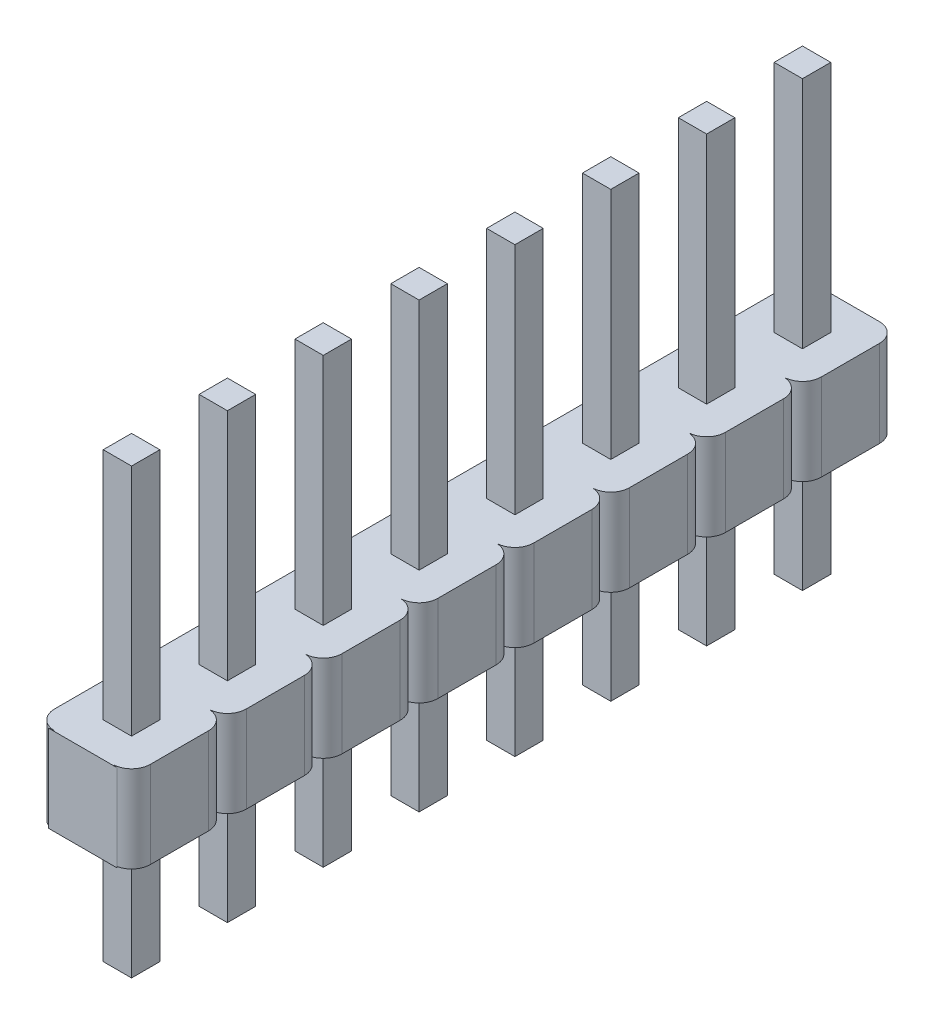
SolidWorks part; units mm, degrees
ref_plane "Alzado" through (0, 0, 0) normal (0, 0, 1) x (1, 0, 0)
ref_plane "Planta" through (0, 0, 0) normal (0, 1, 0) x (1, 0, 0)
ref_plane "Vista lateral" through (0, 0, 0) normal (1, 0, 0) x (0, 0, -1)
ref_plane "Plano1" through (0, 2.3, 0) normal (0, 1, 0) x (1, 0, 0)
sketch "Croquis1" plane through (0, 2.3, 0) normal (0, 1, 0) x (1, 0, 0)
  line L0 (-1.27, -19.07) -> (1.27, -19.07)
  line L1 (1.27, -19.07) -> (1.27, 1.27)
  line L2 (1.27, 1.27) -> (-1.27, 1.27)
  line L3 (-1.27, 1.27) -> (-1.27, -19.07)
extrude "Saliente-Extruir1" add sketch "Croquis1" against normal blind 2.3
sketch "Croquis5" plane through (0, 0, 0) normal (0, -1, 0) x (1, 0, 0)
  line L0 (1.27, 18.55) -> (1.27, 19.55)
  arc A0 (1.27, 19.55) -> (0.77, 19.05) centre (0.77, 19.55) cw
  arc A1 (0.77, 19.05) -> (1.27, 18.55) centre (0.77, 18.55) cw
extrude "Cortar-Extruir4" cut sketch "Croquis5" against normal blind 2.3
sketch "Croquis6" plane through (0, 0, 0) normal (0, -1, 0) x (1, 0, 0)
  line L0 (1.27, 16.01) -> (1.27, 17.01)
  arc A0 (1.27, 17.01) -> (0.77, 16.51) centre (0.77, 17.01) cw
  arc A1 (0.77, 16.51) -> (1.27, 16.01) centre (0.77, 16.01) cw
extrude "Cortar-Extruir5" cut sketch "Croquis6" against normal blind 2.3
sketch "Croquis7" plane through (0, 0, 0) normal (0, -1, 0) x (1, 0, 0)
  line L0 (1.27, 13.47) -> (1.27, 14.47)
  arc A0 (1.27, 14.47) -> (0.77, 13.97) centre (0.77, 14.47) cw
  arc A1 (0.77, 13.97) -> (1.27, 13.47) centre (0.77, 13.47) cw
extrude "Cortar-Extruir6" cut sketch "Croquis7" against normal blind 2.3
sketch "Croquis8" plane through (0, 0, 0) normal (0, -1, 0) x (1, 0, 0)
  line L0 (1.27, 10.93) -> (1.27, 11.93)
  arc A0 (1.27, 11.93) -> (0.77, 11.43) centre (0.77, 11.93) cw
  arc A1 (0.77, 11.43) -> (1.27, 10.93) centre (0.77, 10.93) cw
extrude "Cortar-Extruir7" cut sketch "Croquis8" against normal blind 2.3
sketch "Croquis9" plane through (0, 0, 0) normal (0, -1, 0) x (1, 0, 0)
  line L0 (1.27, 8.39) -> (1.27, 9.39)
  arc A0 (1.27, 9.39) -> (0.77, 8.89) centre (0.77, 9.39) cw
  arc A1 (0.77, 8.89) -> (1.27, 8.39) centre (0.77, 8.39) cw
extrude "Cortar-Extruir8" cut sketch "Croquis9" against normal blind 2.3
sketch "Croquis10" plane through (0, 0, 0) normal (0, -1, 0) x (1, 0, 0)
  line L0 (1.27, 5.85) -> (1.27, 6.85)
  arc A0 (1.27, 6.85) -> (0.77, 6.35) centre (0.77, 6.85) cw
  arc A1 (0.77, 6.35) -> (1.27, 5.85) centre (0.77, 5.85) cw
extrude "Cortar-Extruir9" cut sketch "Croquis10" against normal blind 2.3
sketch "Croquis11" plane through (0, 0, 0) normal (0, -1, 0) x (1, 0, 0)
  line L0 (1.27, 3.31) -> (1.27, 4.31)
  arc A0 (1.27, 4.31) -> (0.77, 3.81) centre (0.77, 4.31) cw
  arc A1 (0.77, 3.81) -> (1.27, 3.31) centre (0.77, 3.31) cw
extrude "Cortar-Extruir10" cut sketch "Croquis11" against normal blind 2.3
sketch "Croquis12" plane through (0, 0, 0) normal (0, -1, 0) x (1, 0, 0)
  line L0 (1.27, 0.77) -> (1.27, 1.77)
  arc A0 (1.27, 1.77) -> (0.77, 1.27) centre (0.77, 1.77) cw
  arc A1 (0.77, 1.27) -> (1.27, 0.77) centre (0.77, 0.77) cw
extrude "Cortar-Extruir11" cut sketch "Croquis12" against normal blind 2.3
sketch "Croquis13" plane through (0, 0, 0) normal (0, -1, 0) x (1, 0, 0)
  line L0 (-1.27, 1.77) -> (-1.27, 0.77)
  arc A0 (-1.27, 0.77) -> (-0.77, 1.27) centre (-0.77, 0.77) cw
  arc A1 (-0.77, 1.27) -> (-1.27, 1.77) centre (-0.77, 1.77) cw
extrude "Cortar-Extruir12" cut sketch "Croquis13" against normal blind 2.3
sketch "Croquis14" plane through (0, 0, 0) normal (0, -1, 0) x (1, 0, 0)
  line L0 (-1.27, 4.31) -> (-1.27, 3.31)
  arc A0 (-1.27, 3.31) -> (-0.77, 3.81) centre (-0.77, 3.31) cw
  arc A1 (-0.77, 3.81) -> (-1.27, 4.31) centre (-0.77, 4.31) cw
extrude "Cortar-Extruir13" cut sketch "Croquis14" against normal blind 2.3
sketch "Croquis15" plane through (0, 0, 0) normal (0, -1, 0) x (1, 0, 0)
  line L0 (-1.27, 6.85) -> (-1.27, 5.85)
  arc A0 (-1.27, 5.85) -> (-0.77, 6.35) centre (-0.77, 5.85) cw
  arc A1 (-0.77, 6.35) -> (-1.27, 6.85) centre (-0.77, 6.85) cw
extrude "Cortar-Extruir14" cut sketch "Croquis15" against normal blind 2.3
sketch "Croquis16" plane through (0, 0, 0) normal (0, -1, 0) x (1, 0, 0)
  line L0 (-1.27, 9.39) -> (-1.27, 8.39)
  arc A0 (-1.27, 8.39) -> (-0.77, 8.89) centre (-0.77, 8.39) cw
  arc A1 (-0.77, 8.89) -> (-1.27, 9.39) centre (-0.77, 9.39) cw
extrude "Cortar-Extruir15" cut sketch "Croquis16" against normal blind 2.3
sketch "Croquis17" plane through (0, 0, 0) normal (0, -1, 0) x (1, 0, 0)
  line L0 (-1.27, 11.93) -> (-1.27, 10.93)
  arc A0 (-1.27, 10.93) -> (-0.77, 11.43) centre (-0.77, 10.93) cw
  arc A1 (-0.77, 11.43) -> (-1.27, 11.93) centre (-0.77, 11.93) cw
extrude "Cortar-Extruir16" cut sketch "Croquis17" against normal blind 2.3
sketch "Croquis18" plane through (0, 0, 0) normal (0, -1, 0) x (1, 0, 0)
  line L0 (-1.27, 14.47) -> (-1.27, 13.47)
  arc A0 (-1.27, 13.47) -> (-0.77, 13.97) centre (-0.77, 13.47) cw
  arc A1 (-0.77, 13.97) -> (-1.27, 14.47) centre (-0.77, 14.47) cw
extrude "Cortar-Extruir17" cut sketch "Croquis18" against normal blind 2.3
sketch "Croquis19" plane through (0, 0, 0) normal (0, -1, 0) x (1, 0, 0)
  line L0 (-1.27, 17.01) -> (-1.27, 16.01)
  arc A0 (-1.27, 16.01) -> (-0.77, 16.51) centre (-0.77, 16.01) cw
  arc A1 (-0.77, 16.51) -> (-1.27, 17.01) centre (-0.77, 17.01) cw
extrude "Cortar-Extruir18" cut sketch "Croquis19" against normal blind 2.3
sketch "Croquis20" plane through (0, 0, 0) normal (0, -1, 0) x (1, 0, 0)
  line L0 (-1.27, 19.55) -> (-1.27, 18.55)
  arc A0 (-1.27, 18.55) -> (-0.77, 19.05) centre (-0.77, 18.55) cw
  arc A1 (-0.77, 19.05) -> (-1.27, 19.55) centre (-0.77, 19.55) cw
extrude "Cortar-Extruir19" cut sketch "Croquis20" against normal blind 2.3
sketch "Croquis24" plane through (0, 0, 0) normal (0, -1, 0) x (1, 0, 0)
  line L0 (-0.375, 0.375) -> (0.375, 0.375)
  line L1 (0.375, 0.375) -> (0.375, -0.375)
  line L2 (0.375, -0.375) -> (-0.375, -0.375)
  line L3 (-0.375, -0.375) -> (-0.375, 0.375)
extrude "Saliente-Extruir2" add sketch "Croquis24" along normal blind 3.25
sketch "Croquis25" plane through (0, 2.3, 0) normal (0, 1, 0) x (-1, 0, 0)
  line L0 (-0.375, 0.375) -> (0.375, 0.375)
  line L1 (0.375, 0.375) -> (0.375, -0.375)
  line L2 (0.375, -0.375) -> (-0.375, -0.375)
  line L3 (-0.375, -0.375) -> (-0.375, 0.375)
extrude "Saliente-Extruir3" add sketch "Croquis25" along normal blind 6.2
sketch "Croquis26" plane through (0, 2.3, 0) normal (0, 1, 0) x (-1, 0, 0)
  line L0 (-0.375, 2.915) -> (0.375, 2.915)
  line L1 (0.375, 2.915) -> (0.375, 2.165)
  line L2 (0.375, 2.165) -> (-0.375, 2.165)
  line L3 (-0.375, 2.165) -> (-0.375, 2.915)
extrude "Saliente-Extruir4" add sketch "Croquis26" along normal blind 6.2
sketch "Croquis27" plane through (0, 2.3, 0) normal (0, 1, 0) x (-1, 0, 0)
  line L0 (-0.375, 4.705) -> (-0.375, 5.455)
  line L1 (-0.375, 5.455) -> (0.375, 5.455)
  line L2 (0.375, 5.455) -> (0.375, 4.705)
  line L3 (0.375, 4.705) -> (-0.375, 4.705)
extrude "Saliente-Extruir5" add sketch "Croquis27" along normal blind 6.2
sketch "Croquis28" plane through (0, 2.3, 0) normal (0, 1, 0) x (-1, 0, 0)
  line L0 (-0.375, 7.245) -> (-0.375, 7.995)
  line L1 (-0.375, 7.995) -> (0.375, 7.995)
  line L2 (0.375, 7.995) -> (0.375, 7.245)
  line L3 (0.375, 7.245) -> (-0.375, 7.245)
extrude "Saliente-Extruir6" add sketch "Croquis28" along normal blind 6.2
sketch "Croquis29" plane through (0, 2.3, 0) normal (0, 1, 0) x (-1, 0, 0)
  line L0 (-0.375, 9.785) -> (-0.375, 10.535)
  line L1 (-0.375, 10.535) -> (0.375, 10.535)
  line L2 (0.375, 10.535) -> (0.375, 9.785)
  line L3 (0.375, 9.785) -> (-0.375, 9.785)
extrude "Saliente-Extruir7" add sketch "Croquis29" along normal blind 6.2
sketch "Croquis30" plane through (0, 2.3, 0) normal (0, 1, 0) x (-1, 0, 0)
  line L0 (-0.375, 12.325) -> (-0.375, 13.075)
  line L1 (-0.375, 13.075) -> (0.375, 13.075)
  line L2 (0.375, 13.075) -> (0.375, 12.325)
  line L3 (0.375, 12.325) -> (-0.375, 12.325)
extrude "Saliente-Extruir8" add sketch "Croquis30" along normal blind 6.2
sketch "Croquis31" plane through (0, 2.3, 0) normal (0, 1, 0) x (-1, 0, 0)
  line L0 (-0.375, 14.865) -> (-0.375, 15.615)
  line L1 (-0.375, 15.615) -> (0.375, 15.615)
  line L2 (0.375, 15.615) -> (0.375, 14.865)
  line L3 (0.375, 14.865) -> (-0.375, 14.865)
extrude "Saliente-Extruir9" add sketch "Croquis31" along normal blind 6.2
sketch "Croquis32" plane through (0, 2.3, 0) normal (0, 1, 0) x (-1, 0, 0)
  line L0 (-0.375, 17.405) -> (-0.375, 18.155)
  line L1 (-0.375, 18.155) -> (0.375, 18.155)
  line L2 (0.375, 18.155) -> (0.375, 17.405)
  line L3 (0.375, 17.405) -> (-0.375, 17.405)
extrude "Saliente-Extruir10" add sketch "Croquis32" along normal blind 6.2
sketch "Croquis37" plane through (0, 0, 0) normal (0, -1, 0) x (1, 0, 0)
  line L0 (-0.375, 2.915) -> (0.375, 2.915)
  line L1 (0.375, 2.915) -> (0.375, 2.165)
  line L2 (0.375, 2.165) -> (-0.375, 2.165)
  line L3 (-0.375, 2.165) -> (-0.375, 2.915)
extrude "Saliente-Extruir15" add sketch "Croquis37" along normal blind 3.25
sketch "Croquis38" plane through (0, 0, 0) normal (0, -1, 0) x (1, 0, 0)
  line L0 (0.375, 5.455) -> (0.375, 4.705)
  line L1 (0.375, 4.705) -> (-0.375, 4.705)
  line L2 (-0.375, 4.705) -> (-0.375, 5.455)
  line L3 (-0.375, 5.455) -> (0.375, 5.455)
extrude "Saliente-Extruir16" add sketch "Croquis38" along normal blind 3.25
sketch "Croquis39" plane through (0, 0, 0) normal (0, -1, 0) x (1, 0, 0)
  line L0 (0.375, 7.995) -> (0.375, 7.245)
  line L1 (0.375, 7.245) -> (-0.375, 7.245)
  line L2 (-0.375, 7.245) -> (-0.375, 7.995)
  line L3 (-0.375, 7.995) -> (0.375, 7.995)
extrude "Saliente-Extruir17" add sketch "Croquis39" along normal blind 3.25
sketch "Croquis40" plane through (0, 0, 0) normal (0, -1, 0) x (1, 0, 0)
  line L0 (0.375, 10.535) -> (0.375, 9.785)
  line L1 (0.375, 9.785) -> (-0.375, 9.785)
  line L2 (-0.375, 9.785) -> (-0.375, 10.535)
  line L3 (-0.375, 10.535) -> (0.375, 10.535)
extrude "Saliente-Extruir18" add sketch "Croquis40" along normal blind 3.25
sketch "Croquis41" plane through (0, 0, 0) normal (0, -1, 0) x (1, 0, 0)
  line L0 (0.375, 13.075) -> (0.375, 12.325)
  line L1 (0.375, 12.325) -> (-0.375, 12.325)
  line L2 (-0.375, 12.325) -> (-0.375, 13.075)
  line L3 (-0.375, 13.075) -> (0.375, 13.075)
extrude "Saliente-Extruir19" add sketch "Croquis41" along normal blind 3.25
sketch "Croquis42" plane through (0, 0, 0) normal (0, -1, 0) x (1, 0, 0)
  line L0 (0.375, 15.615) -> (0.375, 14.865)
  line L1 (0.375, 14.865) -> (-0.375, 14.865)
  line L2 (-0.375, 14.865) -> (-0.375, 15.615)
  line L3 (-0.375, 15.615) -> (0.375, 15.615)
extrude "Saliente-Extruir20" add sketch "Croquis42" along normal blind 3.25
sketch "Croquis43" plane through (0, 0, 0) normal (0, -1, 0) x (1, 0, 0)
  line L0 (0.375, 18.155) -> (0.375, 17.405)
  line L1 (0.375, 17.405) -> (-0.375, 17.405)
  line L2 (-0.375, 17.405) -> (-0.375, 18.155)
  line L3 (-0.375, 18.155) -> (0.375, 18.155)
extrude "Saliente-Extruir21" add sketch "Croquis43" along normal blind 3.25
fillet "Redondeo2" radius 0.5 2 edges at (1.27, 1.15, -1.27) (-1.27, 1.15, -1.27)
